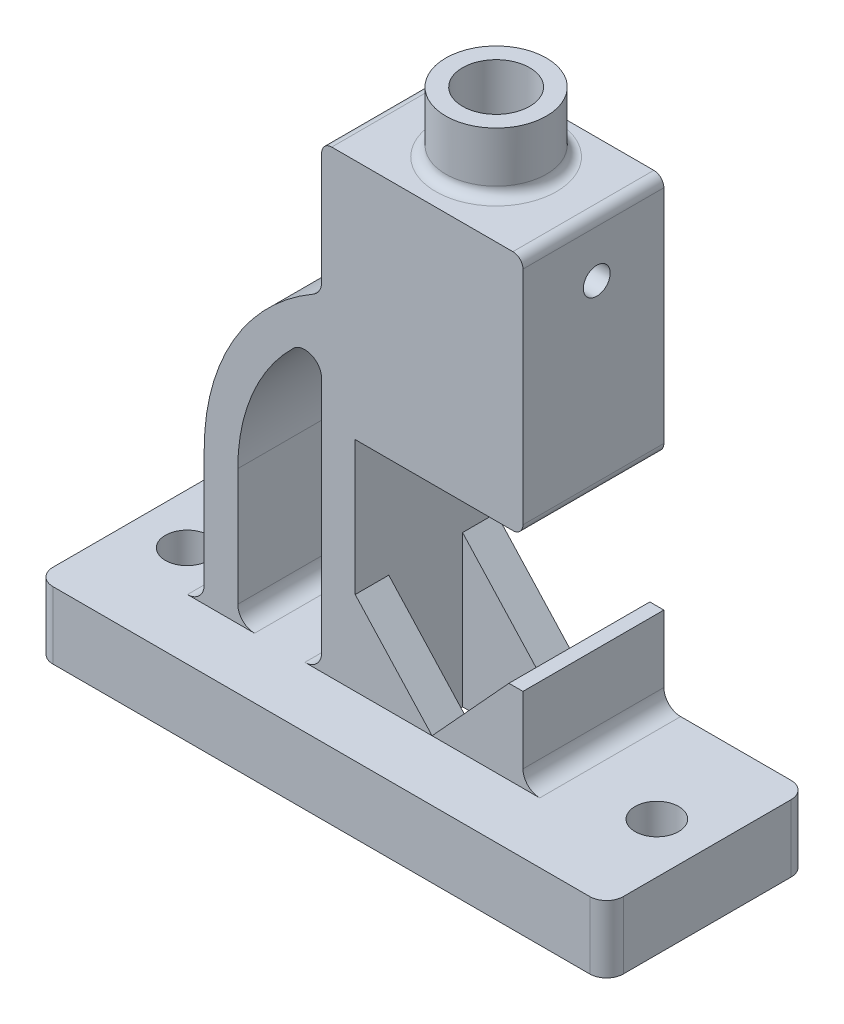
SolidWorks part; units mm, degrees
material "ABS PC"
ref_plane "Front Plane" through (0, 0, 0) normal (0, 0, 1) x (1, 0, 0)
ref_plane "Top Plane" through (0, 0, 0) normal (0, 1, 0) x (1, 0, 0)
ref_plane "Right Plane" through (0, 0, 0) normal (1, 0, 0) x (0, 0, -1)
sketch "Sketch1" plane through (0, 0, 0) normal (0, 1, 0) x (1, 0, 0)
  line L1 (-80, 30) -> (80, 30)
  line L2 (-85, 25) -> (-85, -25)
  line L3 (-80, -30) -> (80, -30)
  line L4 (85, 25) -> (85, -25)
  line L5 (0, -30) -> (0, 30) construction
  line L6 (-85, 0) -> (85, 0) construction
  arc A0 (80, 30) -> (85, 25) centre (80, 25) cw
  arc A1 (80, -30) -> (85, -25) centre (80, -25) ccw
  arc A2 (-80, 30) -> (-85, 25) centre (-80, 25) ccw
  arc A3 (-85, -25) -> (-80, -30) centre (-80, -25) ccw
  point P0 (0, 0)
  point P11 (85, -30)
  point P14 (-85, 30)
  point P17 (-85, -30)
  dimension "D3" = 5
  dimension "D1" = 170
  dimension "D2" = 60
extrude "Boss-Extrude1" add sketch "Sketch1" along normal blind 20
sketch "Sketch2" plane through (0, 0, 0) normal (0, 0, 1) x (1, 0, 0)
  line L0 (-17.9083, 95.7071) -> (-17.9083, 25)
  line L1 (-80, 20) -> (80, 20) construction
  line L2 (-17.9083, 157) -> (42.0917, 157)
  line L3 (42.0917, 157) -> (42.0917, 85)
  line L4 (42.0917, 85) -> (-7.9083, 85)
  line L5 (-7.9083, 85) -> (-7.9083, 45)
  line L6 (-7.9083, 45) -> (15, 20)
  line L7 (15, 20) -> (37.9083, 45)
  line L8 (37.9083, 45) -> (42.0917, 45)
  line L9 (42.0917, 45) -> (42.0917, 25)
  line L10 (15, 20) -> (15, 38.7398) construction
  line L11 (85, 20) -> (85, 0) construction
  line L16 (-42.9083, 25) -> (-42.9083, 60)
  line L17 (-80, 0) -> (80, 0) construction
  line L18 (-52.9083, 25) -> (-52.9083, 60)
  line L19 (-17.9083, 157) -> (-17.9083, 120.6218)
  line L20 (-37.9083, 20) -> (-22.9083, 20)
  line L21 (-42.9083, 20) -> (-42.9083, 60) construction
  line L22 (-57.9083, 20) -> (-58, 20)
  line L23 (-58, 20) -> (-58, 17)
  line L24 (-58, 17) -> (50, 17)
  line L25 (50, 17) -> (50, 20)
  line L26 (50, 20) -> (47.0917, 20)
  line L27 (-52.9083, 20) -> (-52.9083, 60) construction
  arc A0 (-42.9083, 60) -> (-26.4083, 99.2779) centre (12.0917, 60) cw
  arc A1 (-17.9083, 95.7071) -> (-26.4083, 99.2779) centre (-22.9083, 95.7071) ccw
  arc A2 (-52.9083, 60) -> (-20.4083, 116.2917) centre (12.0917, 60) cw
  arc A3 (-52.9083, 60) -> (-33.4083, 106.4193) centre (12.0917, 60) cw construction
  arc A4 (-20.4083, 116.2917) -> (-17.9083, 120.6218) centre (-22.9083, 120.6218) ccw
  arc A5 (-17.9083, 25) -> (-22.9083, 20) centre (-22.9083, 25) cw
  arc A6 (-42.9083, 25) -> (-37.9083, 20) centre (-37.9083, 25) ccw
  arc A7 (42.0917, 25) -> (47.0917, 20) centre (47.0917, 25) ccw
  arc A8 (-52.9083, 25) -> (-57.9083, 20) centre (-57.9083, 25) cw
  point P31 (-17.9083, 20)
  point P36 (-42.9083, 20)
  point P43 (42.0917, 20)
  point P47 (0, 0)
  point P49 (0, 0)
  dimension "D9" = 60
  dimension "D11" = 55
  dimension "D12" = 5
  dimension "D14" = 5
  dimension "D8" = 5
  dimension "D15" = 5
  dimension "D1" = 72
  dimension "D2" = 25
  dimension "D3" = 85
  dimension "D4" = 70
  dimension "D5" = 60
  dimension "D6" = 10
  dimension "D7" = 40
  dimension "D10" = 25
  dimension "D16" = 3
  dimension "D17" = 108
  dimension "D18" = 58
  dimension "D13" = 10
extrude "Boss-Extrude4" add sketch "Sketch2" along normal blind 42 from surface at -30 starting at face at (0, 10, -30)
sketch "Sketch10" plane through (0, 0, 0) normal (0, 1, 0) x (1, 0, 0)
  line L0 (-7.9083, -2) -> (32.0917, -2)
  line L1 (32.0917, -2) -> (32.0917, 20)
  line L2 (32.0917, 20) -> (-7.9083, 20)
  line L4 (42.0917, 30) -> (-7.9083, 30)
  line L5 (42.0917, -12) -> (42.0917, 30)
  line L6 (-7.9083, -12) -> (42.0917, -12)
  line L7 (-7.9083, 30) -> (-7.9083, -12)
  line L8 (42.0917, 30) -> (-7.9083, 30) construction
  line L11 (-7.9083, 20) -> (-7.9083, -2)
  line L12 (-7.9083, -12) -> (42.0917, -12) construction
  line L13 (42.0917, -12) -> (42.0917, 30) construction
  dimension "D1" = 0
  dimension "D2" = 10
extrude "Cut-Extrude3" cut sketch "Sketch10" along normal blind 62 and the other way up to next from surface
sketch "Sketch11" plane through (0, 157, 0) normal (0, 1, 0) x (1, 0, 0)
  line L0 (-17.9083, -12) -> (-17.9083, 30) construction
  line L1 (42.0917, 30) -> (-17.9083, 30) construction
  circle A0 centre (12.0917, 10) radius 15
  dimension "D1" = 30
  dimension "D3" = 30
  dimension "D2" = 20
extrude "Boss-Extrude5" add sketch "Sketch11" along normal blind 18
sketch "Sketch12" plane through (0, 175, 0) normal (0, 1, 0) x (1, 0, 0)
  circle A0 centre (12.0917, 10) radius 10
  dimension "D1" = 20
extrude "Cut-Extrude4" cut sketch "Sketch12" against normal up to next
fillet "Fillet1" radius 3 4 edges at (42.0917, 85, -9) (12.0917, 157, 5) (42.0917, 157, -9) (-17.9083, 157, -9)
sketch "Sketch13" plane through (0, 0, 0) normal (1, 0, 0) x (0, 0, -1)
  line L0 (25, 175) -> (-5, 175) construction
  line L1 (30, 88) -> (30, 154) construction
  circle A0 centre (10, 140) radius 4
  dimension "D1" = 35
  dimension "D2" = 8
  dimension "D3" = 20
extrude "Cut-Extrude5" cut sketch "Sketch13" against normal through all both and the other way through all
sketch "Sketch16" plane through (0, 0, 0) normal (0, 1, 0) x (1, 0, 0)
  line L0 (0, 0) -> (0, 70.7187) construction
  line L1 (80, 30) -> (47.0917, 30) construction
  circle A0 centre (-70, 0) radius 6.5
  circle A1 centre (70, 0) radius 6.5
  point P4 (0, 0)
  dimension "D1" = 140
  dimension "D2" = 13
  dimension "D3" = 30
extrude "Cut-Extrude7" cut sketch "Sketch16" along normal up to next
